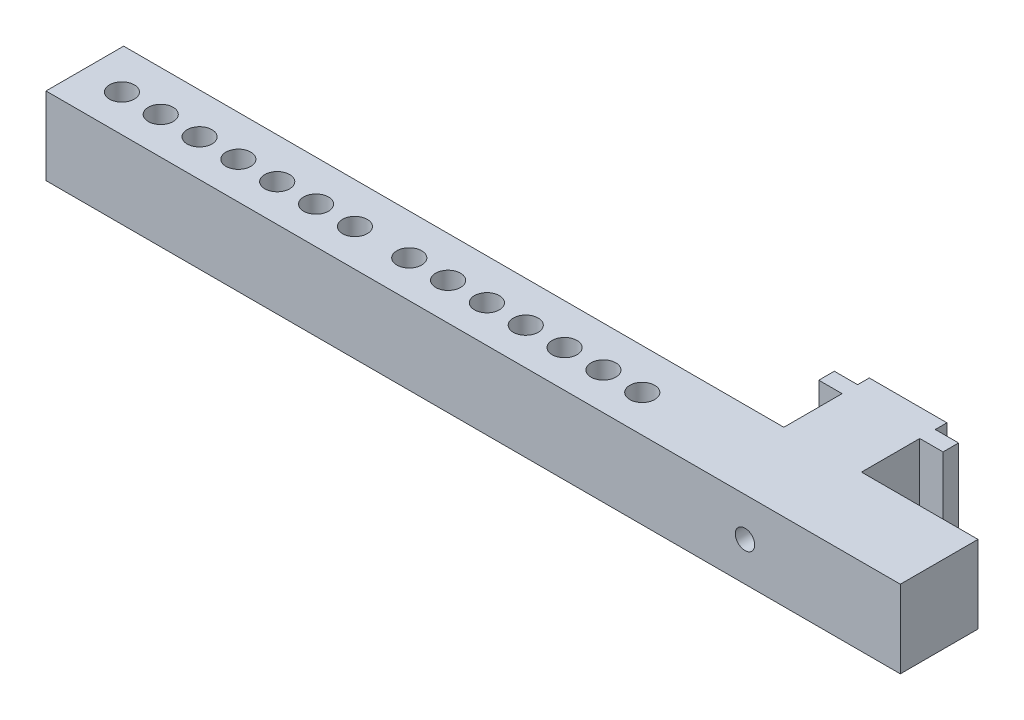
SolidWorks part; units mm, degrees
ref_plane "Front Plane" through (0, 0, 0) normal (0, 0, 1) x (1, 0, 0)
ref_plane "Top Plane" through (0, 0, 0) normal (0, 1, 0) x (1, 0, 0)
ref_plane "Right Plane" through (0, 0, 0) normal (1, 0, 0) x (0, 0, -1)
sketch "Sketch1" plane through (0, 0, 0) normal (0, 0, 1) x (1, 0, 0)
  line L1 (-5, 5) -> (5, 5)
  line L2 (-5, 5) -> (-5, -5)
  line L3 (-5, -5) -> (5, -5)
  line L4 (5, 5) -> (5, -5)
  line L5 (0, -5) -> (0, 5) construction
  line L6 (-5, 0) -> (5, 0) construction
  point P0 (0, 0)
  dimension "D1" = 10
  dimension "D2" = 10
extrude "Boss-Extrude1" add sketch "Sketch1" along normal blind 11
sketch "Sketch2" plane through (5, 0, 0) normal (1, 0, 0) x (0, 0, -1)
  line L0 (-11, -5) -> (0, -5) construction
  line L1 (-3.5, 5) -> (-1.5, 5)
  line L2 (-3.5, 5) -> (-3.5, -5)
  line L3 (-3.5, -5) -> (-1.5, -5)
  line L4 (-1.5, 5) -> (-1.5, -5)
  line L5 (-2.5, -5) -> (-2.5, 5) construction
  line L6 (-3.5, 0) -> (-1.5, 0) construction
  line L7 (-11, -5) -> (-11, 5) construction
  point P0 (-2.5, 0)
  dimension "D1" = 2
  dimension "D2" = 7.5
extrude "Boss-Extrude2" add sketch "Sketch2" along normal blind 3 and the other way blind 13
sketch "Sketch3" plane through (0, 0, 11) normal (0, 0, 1) x (1, 0, 0)
  line L1 (-20, 5) -> (20, 5)
  line L2 (-20, 5) -> (-20, -5)
  line L3 (-20, -5) -> (20, -5)
  line L4 (20, 5) -> (20, -5)
  line L5 (0, -5) -> (0, 5) construction
  line L6 (-20, 0) -> (20, 0) construction
  point P0 (0, 0)
  dimension "D1" = 40
  dimension "D2" = 10
extrude "Boss-Extrude3" add sketch "Sketch3" along normal blind 10
sketch "Sketch5" plane through (-20, 0, 0) normal (-1, 0, 0) x (0, 0, 1)
  line L1 (21, -5) -> (11, -5)
  line L2 (21, -5) -> (21, 5)
  line L3 (21, 5) -> (11, 5)
  line L4 (11, -5) -> (11, 5)
  line L5 (16, 5) -> (16, -5) construction
  line L6 (21, 0) -> (11, 0) construction
  point P0 (16, 0)
  dimension "D1" = 10
  dimension "D2" = 10
extrude "Boss-Extrude4" add sketch "Sketch5" along normal blind 70
hole_wizard "Ø2.5mm Dowel Slot1" positions "Sketch6" profile "Sketch7" size "Ø2.5" standard "ANSI Metric" slot yes end condition through all
sketch "Sketch6" plane through (0, 0, 21) normal (0, 0, 1) x (1, 0, 0)
  point P0 (0, 0)
sketch "Sketch7" plane through (0, 0, 21) normal (1, 0, 0) x (0, -1, 0)
  line L0 (0, 0) -> (0, 21)
  line L1 (0, 21) -> (1.25, 21)
  line L2 (1.25, 21) -> (1.25, 0)
  line L5 (1.25, 0) -> (0, 0)
  line L11 (0, -6.35) -> (0, 107.95) construction
  dimension "Thru Hole Dia." = 2.5
  dimension "Thru Hole Depth" = 21
hole_wizard "Ø3.2 (3.2) Diameter Slot2" positions "Sketch10" profile "Sketch11" size "Ø3.2" standard "ANSI Metric" slot yes end condition through all
sketch "Sketch10" plane through (0, -5, 0) normal (0, -1, 0) x (-1, 0, 0)
  line L0 (90, -11) -> (90, -21) construction
  point P0 (85, -16.2292)
  point P2 (80, -16.2292)
  point P4 (48, -16.2292)
  point P7 (43, -16.2292)
  point P9 (75, -16.2292)
  point P11 (70, -16.2292)
  point P13 (65, -16.2292)
  point P15 (60, -16.2292)
  point P17 (38, -16.2292)
  point P19 (33, -16.2292)
  point P21 (28, -16.2292)
  point P23 (23, -16.2292)
  point P26 (55, -16.2292)
  point P28 (18, -16.2292)
  dimension "D1" = 5
  dimension "D2" = 37
  dimension "D3" = 5
  dimension "D4" = 5
  dimension "D5" = 5
  dimension "D6" = 5
  dimension "D7" = 5
  dimension "D8" = 5
  dimension "D9" = 5
  dimension "D10" = 5
  dimension "D11" = 5
  dimension "D12" = 5
  dimension "D13" = 5
  dimension "D14" = 5
sketch "Sketch11" plane through (-85, -5, 16.2292) normal (1, 0, 0) x (0, 0, -1)
  line L0 (0, 0) -> (0, 10)
  line L1 (0, 10) -> (1.6, 10)
  line L2 (1.6, 10) -> (1.6, 0)
  line L5 (1.6, 0) -> (0, 0)
  line L11 (0, -6.35) -> (0, 107.95) construction
  dimension "Thru Hole Dia." = 3.2
  dimension "Thru Hole Depth" = 10
